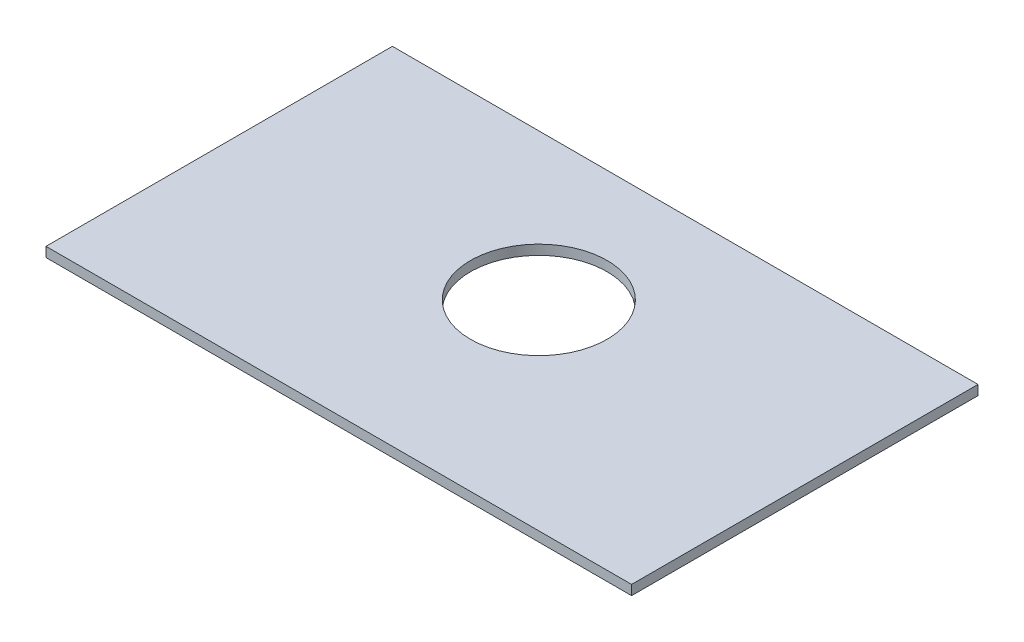
SolidWorks part; units mm, degrees
ref_plane "Front Plane" through (0, 0, 0) normal (0, 0, 1) x (1, 0, 0)
ref_plane "Top Plane" through (0, 0, 0) normal (0, 1, 0) x (1, 0, 0)
ref_plane "Right Plane" through (0, 0, 0) normal (1, 0, 0) x (0, 0, -1)
sketch "Sketch1" plane through (0, 0, 0) normal (0, 1, 0) x (1, 0, 0)
  line L0 (-50.2879, 46.288) -> (-21.1183, 46.288) construction
  line L1 (-50.2879, 99.528) -> (129.7121, 99.528)
  line L2 (-50.2879, 99.528) -> (-50.2879, -6.952)
  line L3 (-50.2879, -6.952) -> (129.7121, -6.952)
  line L4 (129.7121, 99.528) -> (129.7121, -6.952)
  line L5 (39.7121, 99.528) -> (39.7121, 79.6053) construction
  circle A0 centre (39.7121, 54.528) radius 21
  dimension "D3" = 42
  dimension "D1" = 106.48
  dimension "D2" = 180
  dimension "D4" = 45
extrude "Boss-Extrude1" add sketch "Sketch1" along normal blind 3
